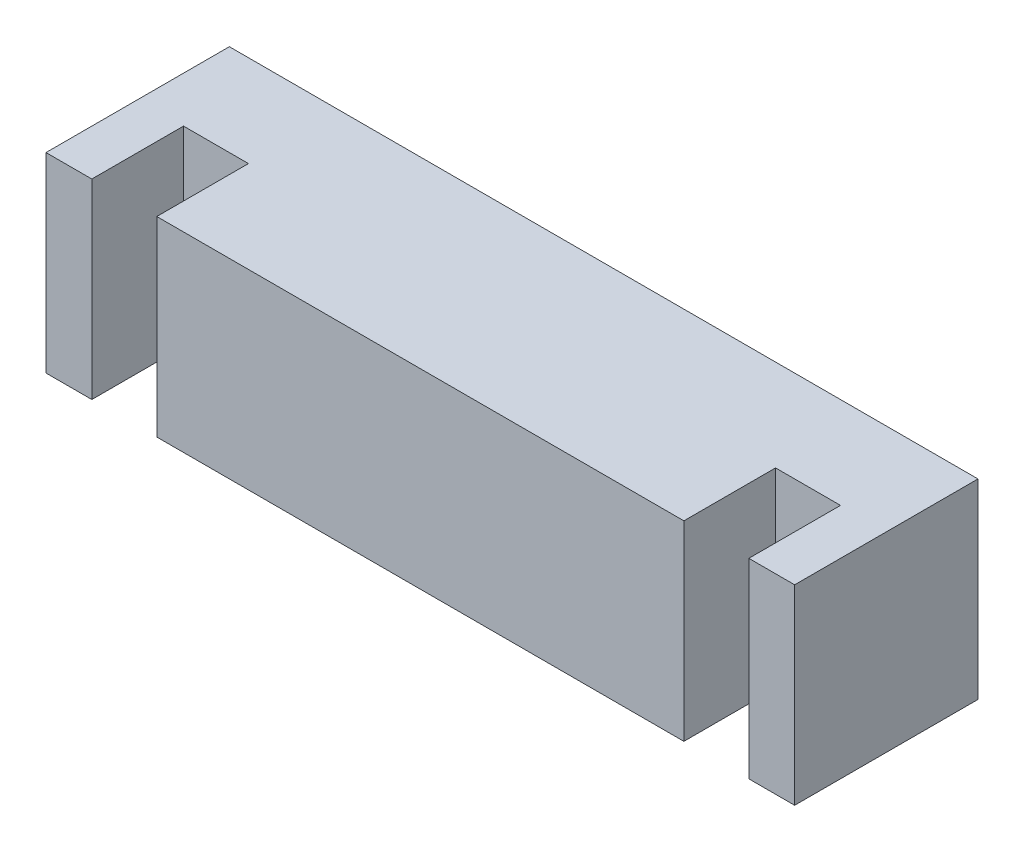
SolidWorks part; units mm, degrees
ref_plane "Front Plane" through (0, 0, 0) normal (0, 0, 1) x (1, 0, 0)
ref_plane "Top Plane" through (0, 0, 0) normal (0, 1, 0) x (1, 0, 0)
ref_plane "Right Plane" through (0, 0, 0) normal (1, 0, 0) x (0, 0, -1)
sketch "Sketch1" plane through (0, 0, 0) normal (0, 0, 1) x (1, 0, 0)
  line L1 (0, 0) -> (19.6, 0)
  line L2 (0, 0) -> (0, 5)
  line L3 (0, 5) -> (19.6, 5)
  line L4 (19.6, 0) -> (19.6, 5)
  dimension "D1" = 19.6
  dimension "D2" = 5
extrude "Boss-Extrude1" add sketch "Sketch1" along normal blind 2.4
sketch "Sketch2" plane through (0, 0, 2.4) normal (0, 0, 1) x (1, 0, 0)
  line L0 (0, 0) -> (19.6, 0) construction
  line L1 (0, 5) -> (1.2, 5)
  line L2 (0, 5) -> (0, 0)
  line L3 (0, 0) -> (1.2, 0)
  line L4 (1.2, 5) -> (1.2, 0)
  line L5 (19.6, 5) -> (0, 5) construction
  line L6 (19.6, 0) -> (18.4, 0)
  line L7 (19.6, 0) -> (19.6, 5)
  line L8 (19.6, 5) -> (18.4, 5)
  line L9 (18.4, 0) -> (18.4, 5)
  line L10 (9.8, 5) -> (9.8, 0) construction
  line L11 (2.9, 0) -> (16.7, 0)
  line L12 (2.9, 0) -> (2.9, 5)
  line L13 (2.9, 5) -> (16.7, 5)
  line L14 (16.7, 0) -> (16.7, 5)
  line L15 (2.9, 0) -> (16.7, 5) construction
  line L16 (2.9, 5) -> (16.7, 0) construction
  point P14 (9.8, 5)
  point P15 (9.8, 2.5)
  point P20 (0, 0)
  dimension "D1" = 1.2
  dimension "D2" = 1.2
  dimension "D3" = 13.8
extrude "Boss-Extrude2" add sketch "Sketch2" along normal blind 2.4
